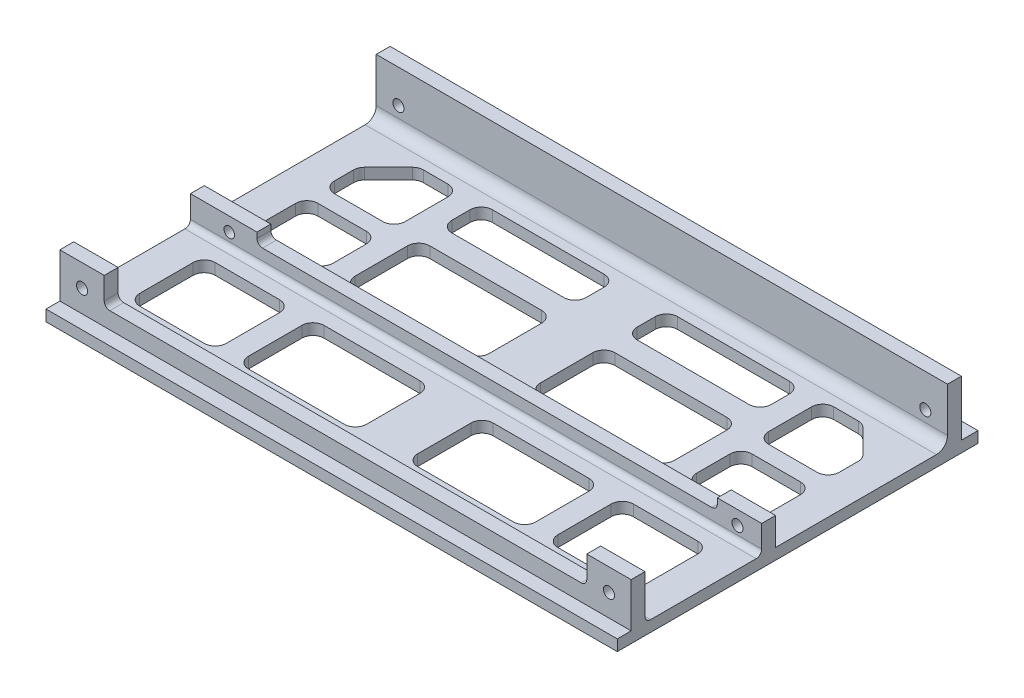
SolidWorks part; units mm, degrees
ref_plane "Front Plane" through (0, 0, 0) normal (0, 0, 1) x (1, 0, 0)
ref_plane "Top Plane" through (0, 0, 0) normal (0, 1, 0) x (1, 0, 0)
ref_plane "Right Plane" through (0, 0, 0) normal (1, 0, 0) x (0, 0, -1)
sketch "Sketch1" plane through (0, 0, 0) normal (0, 1, 0) x (1, 0, 0)
  line L1 (-51.5, -31.02) -> (51.5, -31.02)
  line L2 (-51.5, -31.02) -> (-51.5, 31.02)
  line L3 (-51.5, 31.02) -> (51.5, 31.02)
  line L4 (51.5, -31.02) -> (51.5, 31.02)
  line L5 (-51.5, -31.02) -> (51.5, 31.02) construction
  line L6 (-51.5, 31.02) -> (51.5, -31.02) construction
  point P0 (0, 0)
  point P6 (0, 0)
  dimension "D1" = 62.04
  dimension "D2" = 103
extrude "Boss-Extrude1" add sketch "Sketch1" along normal blind 2
sketch "Sketch2" plane through (0, 0, -31.02) normal (0, 0, -1) x (-1, 0, 0)
  line L4 (-51.5, 0) -> (51.5, 0)
  line L5 (51.5, 0) -> (51.5, 2)
  line L6 (51.5, 2) -> (-51.5, 2)
  line L7 (-51.5, 2) -> (-51.5, 0)
  line L8 (-51.5, 0) -> (51.5, 0)
  line L9 (51.5, 0) -> (51.5, 2)
  line L10 (51.5, 2) -> (-51.5, 2)
  line L11 (-51.5, 2) -> (-51.5, 0)
  dimension "D1" = 0
extrude "Boss-Extrude2" add sketch "Sketch2" along normal blind 3
sketch "Sketch5" plane through (0, 2, 0) normal (0, 1, 0) x (1, 0, 0)
  line L0 (51.5, 31.02) -> (43.5, 31.02)
  line L1 (51.5, -31.02) -> (51.5, 34.02) construction
  line L2 (43.5, 31.02) -> (43.5, 28.52)
  line L3 (43.5, 28.52) -> (51.5, 28.52)
  line L4 (51.5, 28.52) -> (51.5, 31.02)
  line L5 (0, -38.0579) -> (0, 51.3631) construction
  line L6 (-51.5, 34.02) -> (51.5, 34.02) construction
  dimension "D1" = 3
  dimension "D2" = 2.5
  dimension "D3" = 8
extrude "Boss-Extrude4" add sketch "Sketch5" along normal blind 10
sketch "Sketch6" plane through (0, 2, 0) normal (0, 1, 0) x (1, 0, 0)
  line L0 (43.5, 28.52) -> (0, 28.52)
  line L1 (0, 30.9258) -> (43.5, 31.02)
  line L2 (43.5, 31.02) -> (43.5, 28.52)
  line L3 (0, 28.52) -> (0, 30.9258)
extrude "Boss-Extrude5" add sketch "Sketch6" along normal blind 10
ref_plane "Plane1" through (0, 0, 0) normal (1, 0, 0) x (0, 0, -1)
sketch "Sketch7" plane through (0, 0, -28.52) normal (0, 0, 1) x (1, 0, 0)
  line L0 (0, 2) -> (51.5, 2) construction
  line L1 (51.5, 12) -> (51.5, 2) construction
  circle A0 centre (47.5, 6) radius 1
  dimension "D1" = 2
  dimension "D2" = 4
  dimension "D3" = 4
extrude "Cut-Extrude1" cut sketch "Sketch7" against normal blind 3
mirror "Mirror1" about plane through (0, 0, 0) normal (1, 0, 0) of "Boss-Extrude5", "Cut-Extrude1", "Boss-Extrude4"
fillet "Fillet2" radius 2 1 edges at (0, 2, -28.52)
sketch "Sketch8" plane through (0, 2, 0) normal (0, 1, 0) x (1, 0, 0)
  line L0 (51.5, -4.98) -> (-51.5, -4.98)
  line L3 (-51.5, -4.98) -> (-51.5, -2.48)
  line L4 (-51.5, -2.48) -> (51.5, -2.48)
  line L5 (51.5, -2.48) -> (51.5, -4.98)
  line L10 (-51.5, -31.02) -> (51.5, -31.02) construction
  point P2 (0, 0)
  point P3 (0, 0)
  point P10 (0, 0)
  dimension "D1" = 2.5
  dimension "D2" = 2.5
  dimension "D3" = 26.04
extrude "Boss-Extrude6" add sketch "Sketch8" along normal blind 3
sketch "Sketch9" plane through (0, 5, 0) normal (0, 1, 0) x (1, 0, 0)
  line L0 (51.5, -4.98) -> (43.5, -4.98)
  line L1 (-51.5, -4.98) -> (51.5, -4.98) construction
  line L2 (43.5, -4.98) -> (43.5, -2.48)
  line L3 (51.5, -2.48) -> (-51.5, -2.48) construction
  line L4 (43.5, -2.48) -> (51.5, -2.48)
  line L5 (51.5, -2.48) -> (51.5, -4.98)
  dimension "D1" = 8
extrude "Boss-Extrude7" add sketch "Sketch9" along normal blind 2
sketch "Sketch11" plane through (0, 0, 4.98) normal (0, 0, 1) x (1, 0, 0)
  line L1 (51.5, 7) -> (51.5, 2) construction
  circle A0 centre (47.13, 4.5) radius 1
  point P3 (0, 0)
  dimension "D1" = 2
  dimension "D2" = 4.37
extrude "Cut-Extrude3" cut sketch "Sketch11" against normal blind 22
fillet "Fillet4" radius 1 1 edges at (0, 2, 4.98)
sketch "Sketch12" plane through (0, 5, 0) normal (0, 1, 0) x (1, 0, 0)
  line L0 (-51.5, -4.98) -> (-39.5, -4.98)
  line L1 (-51.5, -4.98) -> (43.5, -4.98) construction
  line L2 (-39.5, -4.98) -> (-39.5, -2.48)
  line L3 (43.5, -2.48) -> (-51.5, -2.48) construction
  line L4 (-39.5, -2.48) -> (-51.5, -2.48)
  line L5 (-51.5, -2.48) -> (-51.5, -4.98)
  dimension "D1" = 12
extrude "Boss-Extrude8" add sketch "Sketch12" along normal blind 2
fillet "Fillet5" radius 1 1 edges at (-39.5, 5, 3.73)
sketch "Sketch13" plane through (0, 0, 4.98) normal (0, 0, 1) x (1, 0, 0)
  line L0 (-51.5, 7) -> (-51.5, 3) construction
  line L1 (-51.5, 7) -> (-39.5, 7) construction
  circle A0 centre (-44.5, 4.5) radius 0.9513
  point P2 (0, 0)
  point P5 (0, 0)
  dimension "D1" = 7
  dimension "D2" = 2.5
extrude "Cut-Extrude4" cut sketch "Sketch13" against normal blind 12
fillet "Fillet6" radius 1 1 edges at (43.5, 5, 3.73)
sketch "Sketch14" plane through (0, 2, 0) normal (0, 1, 0) x (1, 0, 0)
  line L0 (51.5, -28.52) -> (-51.5, -28.52)
  line L1 (-51.5, -28.52) -> (-51.5, -26.02)
  line L2 (-51.5, -5.98) -> (-51.5, -31.02) construction
  line L3 (-51.5, -26.02) -> (51.5, -26.02)
  line L4 (51.5, -31.02) -> (51.5, -5.98) construction
  line L5 (51.5, -26.02) -> (51.5, -28.52)
  line L6 (-51.5, -31.02) -> (51.5, -31.02) construction
  dimension "D1" = 2.5
  dimension "D2" = 2.5
extrude "Boss-Extrude9" add sketch "Sketch14" along normal blind 3
sketch "Sketch15" plane through (0, 5, 0) normal (0, 1, 0) x (1, 0, 0)
  line L0 (51.5, -28.52) -> (43.5, -28.52)
  line L1 (-51.5, -28.52) -> (51.5, -28.52) construction
  line L2 (43.5, -28.52) -> (43.5, -26.02)
  line L3 (51.5, -26.02) -> (-51.5, -26.02) construction
  line L4 (43.5, -26.02) -> (51.5, -26.02)
  line L5 (51.5, -26.02) -> (51.5, -28.52)
  line L6 (-51.5, -28.52) -> (-51.5, -26.02)
  line L7 (-51.5, -26.02) -> (-43.5, -26.02)
  line L8 (-43.5, -26.02) -> (-43.5, -28.52)
  line L9 (-43.5, -28.52) -> (-51.5, -28.52)
  point P14 (0, 0)
  point P17 (0, 0)
  point P18 (51.5, -31.02)
  point P19 (0, 0)
  point P21 (0, 0)
  dimension "D1" = 8
  dimension "D2" = 8
  dimension "D3" = 2.5
extrude "Boss-Extrude10" add sketch "Sketch15" along normal blind 5
sketch "Sketch16" plane through (0, 0, 31.02) normal (0, 0, 1) x (1, 0, 0)
  line L0 (43.5, 10) -> (51.5, 10) construction
  line L2 (51.5, 2) -> (51.5, 0) construction
  line L3 (-51.5, 2) -> (-51.5, 0) construction
  line L4 (-51.5, 10) -> (-43.5, 10) construction
  circle A0 centre (47.5, 6) radius 1
  circle A1 centre (-47.5, 6) radius 1
  dimension "D5" = 2
  dimension "D6" = 2
  dimension "D1" = 4
  dimension "D2" = 4
  dimension "D3" = 4
  dimension "D4" = 4
extrude "Cut-Extrude5" cut sketch "Sketch16" against normal blind 15
fillet "Fillet7" radius 1 3 edges at (0, 2, 26.02) (43.5, 5, 27.27) (-43.5, 5, 27.27)
sketch "Sketch17" plane through (0, 2, 0) normal (0, 1, 0) x (1, 0, 0)
  line L0 (43.5, -22.1211) -> (31.8853, -22.1211)
  line L1 (29.8853, -20.1211) -> (29.8853, -10.5043)
  line L2 (31.8853, -8.5043) -> (43.5, -8.5043)
  line L3 (45.5, -10.5043) -> (45.5, -20.1211)
  line L4 (25.8853, -20.1211) -> (25.8853, -10.5043)
  line L5 (23.8853, -8.5043) -> (6.6087, -8.5043)
  line L6 (4.6087, -10.5043) -> (4.6087, -20.1211)
  line L7 (6.6087, -22.1211) -> (23.8853, -22.1211)
  line L8 (44.9142, 19.849) -> (40.6192, 24.144)
  line L9 (39.205, 24.7298) -> (34.7808, 24.7298)
  line L10 (32.7808, 22.7298) -> (32.7808, 15.003)
  line L11 (34.7808, 13.003) -> (43.5, 13.003)
  line L12 (45.5, 15.003) -> (45.5, 18.4348)
  line L13 (43.5, 10.003) -> (34.7808, 10.003)
  line L14 (32.7808, 8.003) -> (32.7808, 2)
  line L15 (34.7808, 0) -> (43.5, 0)
  line L16 (45.5, 2) -> (45.5, 8.003)
  line L17 (28.7808, 2) -> (28.7808, 11.4521)
  line L18 (26.7808, 13.4521) -> (6.6087, 13.4521)
  line L19 (4.6087, 11.4521) -> (4.6087, 2)
  line L20 (6.6087, 0) -> (26.7808, 0)
  line L21 (28.7808, 19.4521) -> (28.7808, 22.7298)
  line L22 (26.7808, 24.7298) -> (6.6087, 24.7298)
  line L23 (4.6087, 22.7298) -> (4.6087, 19.4521)
  line L24 (6.6087, 17.4521) -> (26.7808, 17.4521)
  line L25 (51.5, -25.02) -> (51.5, -5.98) construction
  line L26 (51.5, -2.48) -> (51.5, 26.52) construction
  arc A0 (4.6087, 2) -> (6.6087, 0) centre (6.6087, 2) ccw
  arc A1 (28.7808, 2) -> (26.7808, 0) centre (26.7808, 2) cw
  arc A2 (28.7808, 11.4521) -> (26.7808, 13.4521) centre (26.7808, 11.4521) ccw
  arc A3 (6.6087, 13.4521) -> (4.6087, 11.4521) centre (6.6087, 11.4521) ccw
  arc A4 (4.6087, 19.4521) -> (6.6087, 17.4521) centre (6.6087, 19.4521) ccw
  arc A5 (6.6087, 24.7298) -> (4.6087, 22.7298) centre (6.6087, 22.7298) ccw
  arc A6 (28.7808, 22.7298) -> (26.7808, 24.7298) centre (26.7808, 22.7298) ccw
  arc A7 (28.7808, 19.4521) -> (26.7808, 17.4521) centre (26.7808, 19.4521) cw
  arc A8 (32.7808, 15.003) -> (34.7808, 13.003) centre (34.7808, 15.003) ccw
  arc A9 (34.7808, 24.7298) -> (32.7808, 22.7298) centre (34.7808, 22.7298) ccw
  arc A10 (40.6192, 24.144) -> (39.205, 24.7298) centre (39.205, 22.7298) ccw
  arc A11 (44.9142, 19.849) -> (45.5, 18.4348) centre (43.5, 18.4348) cw
  arc A12 (43.5, 13.003) -> (45.5, 15.003) centre (43.5, 15.003) ccw
  arc A13 (32.7808, 2) -> (34.7808, 0) centre (34.7808, 2) ccw
  arc A14 (34.7808, 10.003) -> (32.7808, 8.003) centre (34.7808, 8.003) ccw
  arc A15 (43.5, 10.003) -> (45.5, 8.003) centre (43.5, 8.003) cw
  arc A16 (43.5, 0) -> (45.5, 2) centre (43.5, 2) ccw
  arc A17 (4.6087, -20.1211) -> (6.6087, -22.1211) centre (6.6087, -20.1211) ccw
  arc A18 (6.6087, -8.5043) -> (4.6087, -10.5043) centre (6.6087, -10.5043) ccw
  arc A19 (25.8853, -10.5043) -> (23.8853, -8.5043) centre (23.8853, -10.5043) ccw
  arc A20 (25.8853, -20.1211) -> (23.8853, -22.1211) centre (23.8853, -20.1211) cw
  arc A21 (31.8853, -22.1211) -> (29.8853, -20.1211) centre (31.8853, -20.1211) cw
  arc A22 (29.8853, -10.5043) -> (31.8853, -8.5043) centre (31.8853, -10.5043) cw
  arc A23 (43.5, -8.5043) -> (45.5, -10.5043) centre (43.5, -10.5043) cw
  arc A24 (43.5, -22.1211) -> (45.5, -20.1211) centre (43.5, -20.1211) ccw
  point P30 (29.8853, -15.3127)
  point P37 (28.7808, 13.4521)
  point P40 (4.6087, 13.4521)
  point P71 (4.6087, -8.5043)
  dimension "D9" = 2
  dimension "D1" = 6
  dimension "D2" = 6
  dimension "D3" = 6
  dimension "D4" = 4
  dimension "D5" = 4
  dimension "D6" = 4
  dimension "D7" = 4
  dimension "D8" = 3
extrude "Cut-Extrude6" cut sketch "Sketch17" against normal blind 5
mirror "Mirror4" about plane through (0, 0, 0) normal (1, 0, 0) of "Cut-Extrude6"
